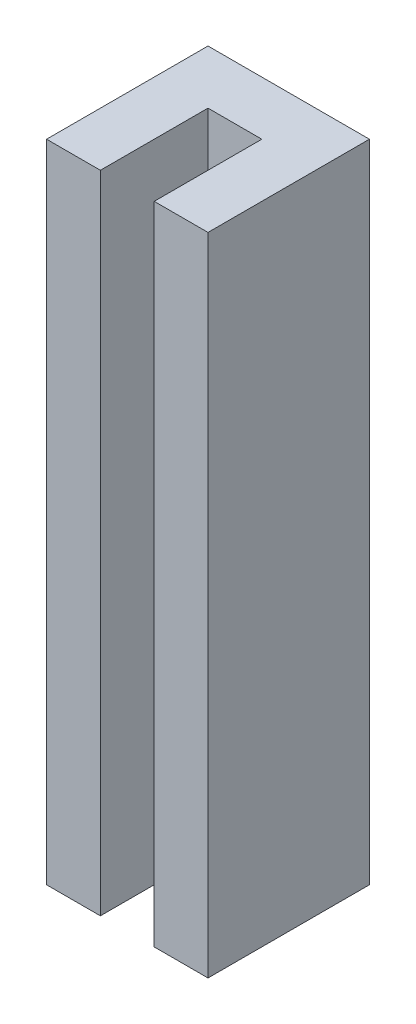
SolidWorks part; units mm, degrees
material "6061 Alloy"
ref_plane "Front Plane" through (0, 0, 0) normal (0, 0, 1) x (1, 0, 0)
ref_plane "Top Plane" through (0, 0, 0) normal (0, 1, 0) x (1, 0, 0)
ref_plane "Right Plane" through (0, 0, 0) normal (1, 0, 0) x (0, 0, -1)
sketch "Sketch1" plane through (0, 0, 0) normal (0, 1, 0) x (1, 0, 0)
  line L1 (-4.7625, -4.7625) -> (-1.5875, -4.7625)
  line L2 (-4.7625, -4.7625) -> (-4.7625, 4.7625)
  line L3 (-4.7625, 4.7625) -> (4.7625, 4.7625)
  line L4 (4.7625, -4.7625) -> (4.7625, 4.7625)
  line L5 (-4.7625, -4.7625) -> (4.7625, 4.7625) construction
  line L6 (-4.7625, 4.7625) -> (4.7625, -4.7625) construction
  line L7 (-1.5875, 1.5875) -> (1.5875, 1.5875)
  line L8 (-1.5875, 1.5875) -> (-1.5875, -4.7625)
  line L9 (1.5875, -4.7625) -> (4.7625, -4.7625)
  line L10 (1.5875, 1.5875) -> (1.5875, -4.7625)
  point P0 (0, 0)
  dimension "D1" = 3.175
  dimension "D2" = 3.175
  dimension "D3" = 9.525
  dimension "D4" = 3.175
  dimension "D5" = 9.525
extrude "Extrude1" add sketch "Sketch1" along normal mid plane 38.1
hole_wizard "#4-40 Tapped Hole1" positions "3DSketch1" profile "Sketch3" tap size "#4-40" standard "Ansi Inch"
sketch3d "3DSketch1"
  line L0 (0, 19.05, -4.7625) -> (0, 7.9375, -4.7625) construction
  line L1 (4.7625, 19.05, -4.7625) -> (-4.7625, 19.05, -4.7625) construction
  point P0 (0, 7.9375, -4.7625)
  point P2 (0, -14.2875, -4.7625)
  dimension "D1" = 22.225
  dimension "D2" = 11.1125
sketch "Sketch3" plane through (0, 7.9375, -4.7625) normal (1, 0, 0) x (0, 1, 0)
  line L0 (0, 0) -> (0, 9.5692)
  line L1 (0, 9.5692) -> (1.1303, 8.89)
  line L2 (1.1303, 8.89) -> (1.1303, 5.588)
  line L3 (1.1303, 5.588) -> (1.4224, 5.588)
  line L4 (1.4224, 5.588) -> (1.4224, 0)
  line L5 (1.4224, 0) -> (0, 0)
  line L10 (0, 9.5692) -> (-1.1303, 8.89) construction
  line L11 (0, -6.35) -> (0, 107.95) construction
  dimension "Tap Drill Dia." = 2.2606
  dimension "Tap Drill Depth" = 8.89
  dimension "Thread Major Dia." = 2.8448
  dimension "Thread Depth" = 5.588
  dimension "Drill Angle" = 118
